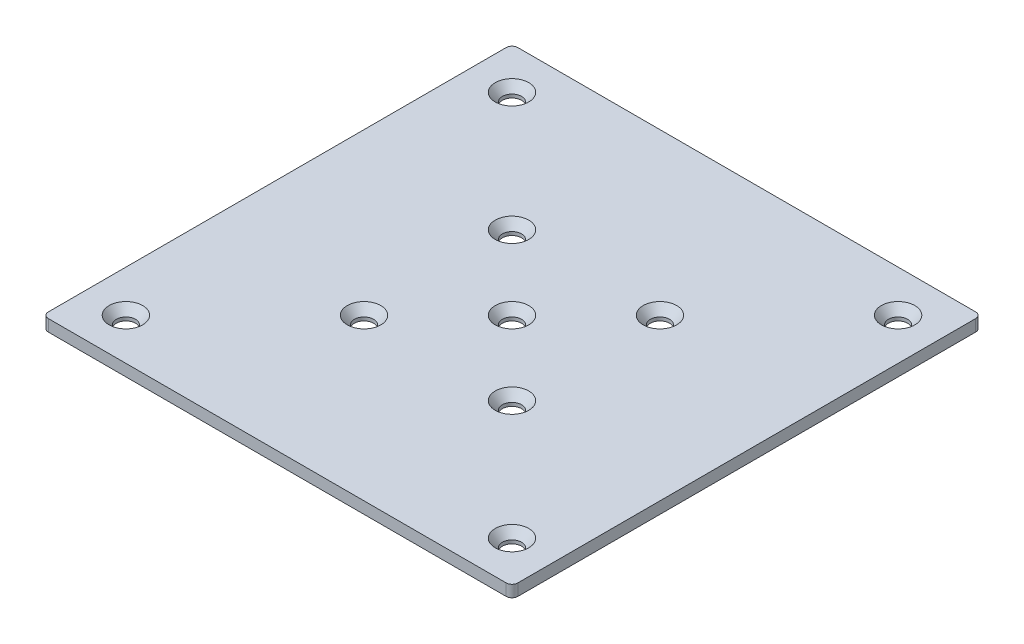
SolidWorks part; units mm, degrees
ref_plane "Plan de face" through (0, 0, 0) normal (0, 0, 1) x (1, 0, 0)
ref_plane "Plan de dessus" through (0, 0, 0) normal (0, 1, 0) x (1, 0, 0)
ref_plane "Plan de droite" through (0, 0, 0) normal (1, 0, 0) x (0, 0, -1)
sketch "Esquisse1" plane through (0, 0, 0) normal (0, 1, 0) x (1, 0, 0)
  line L1 (-40, -40) -> (40, -40)
  line L2 (-40, -40) -> (-40, 40)
  line L3 (-40, 40) -> (40, 40)
  line L4 (40, -40) -> (40, 40)
  line L5 (-40, -40) -> (40, 40) construction
  line L6 (-40, 40) -> (40, -40) construction
  point P0 (0, 0)
  dimension "D1" = 80
  dimension "D2" = 80
extrude "Boss.-Extru.1" add sketch "Esquisse1" along normal blind 2
sketch "Esquisse2" plane through (0, 2, 0) normal (0, 1, 0) x (1, 0, 0)
  line L0 (-40, 40) -> (40, -40) construction
  line L1 (-40, -40) -> (40, 40) construction
  line L3 (-32.8975, -32.8975) -> (32.8975, -32.8975) construction
  line L4 (-32.8975, -32.8975) -> (-32.8975, 32.8975) construction
  line L5 (-32.8975, 32.8975) -> (32.8975, 32.8975) construction
  line L6 (32.8975, -32.8975) -> (32.8975, 32.8975) construction
  line L7 (-32.8975, -32.8975) -> (32.8975, 32.8975) construction
  line L8 (-32.8975, 32.8975) -> (32.8975, -32.8975) construction
  line L9 (-12.6063, -12.6063) -> (12.6063, -12.6063) construction
  line L10 (-12.6063, -12.6063) -> (-12.6063, 12.6063) construction
  line L11 (-12.6063, 12.6063) -> (12.6063, 12.6063) construction
  line L12 (12.6063, -12.6063) -> (12.6063, 12.6063) construction
  line L13 (-12.6063, -12.6063) -> (12.6063, 12.6063) construction
  line L14 (-12.6063, 12.6063) -> (12.6063, -12.6063) construction
  point P8 (0, 0)
  point P14 (0, 0)
hole_wizard "Fraisage pour vis à tête fraisée bombée #41" positions "Esquisse5" profile "Esquisse3" countersink size "#4" standard "Ansi Inch" end condition through all
sketch "Esquisse5" plane through (0, 2, 0) normal (0, 1, 0) x (1, 0, 0)
  point P0 (-32.8975, 32.8975)
  point P3 (32.8975, 32.8975)
  point P6 (32.8975, -32.8975)
  point P9 (-32.8975, -32.8975)
sketch "Esquisse3" plane through (-32.8975, 2, -32.8975) normal (1, 0, 0) x (0, 0, 1)
  line L0 (0, 0) -> (0, 2)
  line L1 (0, 2) -> (1.6319, 2)
  line L2 (1.6319, 2) -> (1.6319, 1.4098)
  line L3 (1.6319, 1.4098) -> (2.8575, 0)
  line L5 (2.8575, 0) -> (0, 0)
  line L6 (-1.6319, 1.4098) -> (-2.8575, 0) construction
  line L11 (0, -6.35) -> (0, 107.95) construction
  dimension "Diamètre du perçage jusqu'au prochain" = 3.2639
  dimension "Profondeur du perçage jusqu'au prochain" = 2
  dimension "Diamètre du fraisage entrant" = 5.715
  dimension "Angle du fraisage entrant" = 82
hole_wizard "Fraisage pour vis à tête fraisée bombée #42" positions "Esquisse7" profile "Esquisse6" countersink size "#4" standard "Ansi Inch" end condition through all
sketch "Esquisse7" plane through (0, 2, 0) normal (0, 1, 0) x (1, 0, 0)
  point P0 (0, 0)
sketch "Esquisse6" plane through (0, 2, 0) normal (1, 0, 0) x (0, 0, 1)
  line L0 (0, 0) -> (0, 2)
  line L1 (0, 2) -> (1.6319, 2)
  line L2 (1.6319, 2) -> (1.6319, 1.4098)
  line L3 (1.6319, 1.4098) -> (2.8575, 0)
  line L5 (2.8575, 0) -> (0, 0)
  line L6 (-1.6319, 1.4098) -> (-2.8575, 0) construction
  line L11 (0, -6.35) -> (0, 107.95) construction
  dimension "Diamètre du perçage jusqu'au prochain" = 3.2639
  dimension "Profondeur du perçage jusqu'au prochain" = 2
  dimension "Diamètre du fraisage entrant" = 5.715
  dimension "Angle du fraisage entrant" = 82
hole_wizard "Fraisage pour vis à tête fraisée bombée #43" positions "Esquisse9" profile "Esquisse8" countersink size "#4" standard "Ansi Inch" end condition through all
sketch "Esquisse9" plane through (0, 2, 0) normal (0, 1, 0) x (1, 0, 0)
  point P0 (-12.6063, 12.6063)
  point P3 (12.6063, 12.6063)
  point P6 (12.6063, -12.6063)
  point P9 (-12.6063, -12.6063)
sketch "Esquisse8" plane through (-12.6063, 2, -12.6063) normal (1, 0, 0) x (0, 0, 1)
  line L0 (0, 0) -> (0, 2)
  line L1 (0, 2) -> (1.6319, 2)
  line L2 (1.6319, 2) -> (1.6319, 1.4098)
  line L3 (1.6319, 1.4098) -> (2.8575, 0)
  line L5 (2.8575, 0) -> (0, 0)
  line L6 (-1.6319, 1.4098) -> (-2.8575, 0) construction
  line L11 (0, -6.35) -> (0, 107.95) construction
  dimension "Diamètre du perçage jusqu'au prochain" = 3.2639
  dimension "Profondeur du perçage jusqu'au prochain" = 2
  dimension "Diamètre du fraisage entrant" = 5.715
  dimension "Angle du fraisage entrant" = 82
fillet "Congé1" radius 1 1 edges at (-40, 1, 40)
fillet "Congé2" radius 1 3 edges at (40, 1, 40) (40, 1, -40) (-40, 1, -40)
